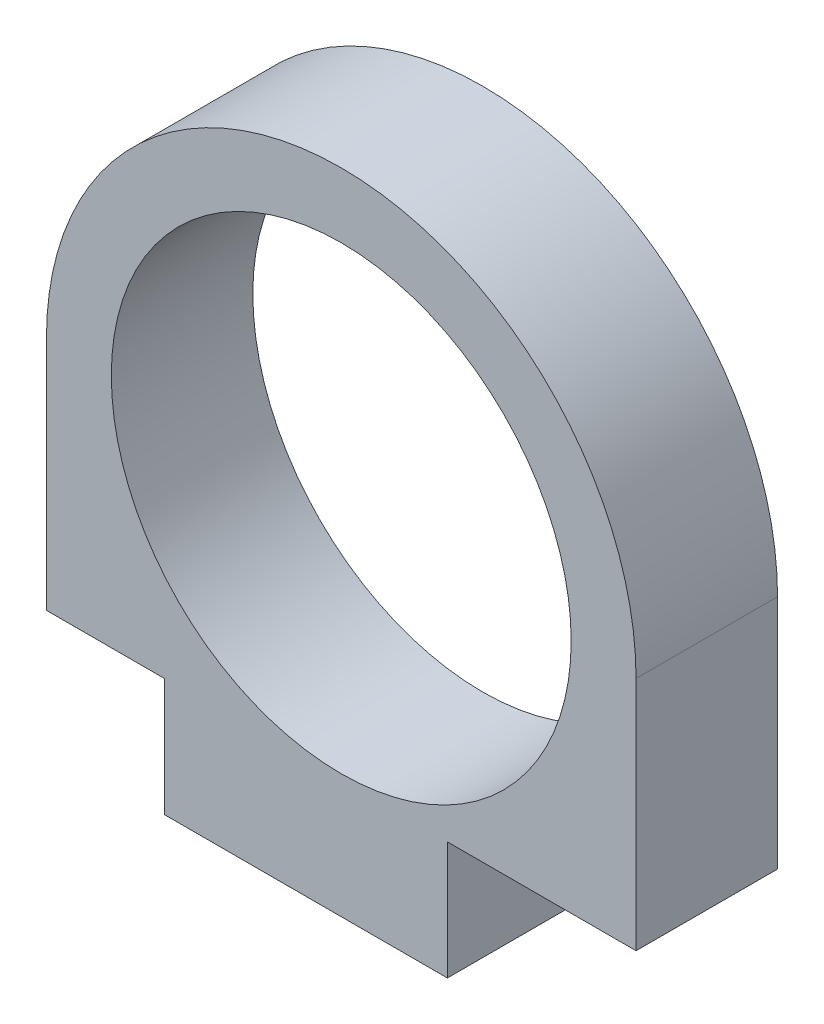
SolidWorks part; units mm, degrees
ref_plane "Alzado" through (0, 0, 0) normal (0, 0, 1) x (1, 0, 0)
ref_plane "Planta" through (0, 0, 0) normal (0, 1, 0) x (1, 0, 0)
ref_plane "Vista lateral" through (0, 0, 0) normal (1, 0, 0) x (0, 0, -1)
sketch "Croquis1" plane through (0, 0, 0) normal (0, 0, 1) x (1, 0, 0)
  line L0 (-12.5, -10) -> (12.5, -10) construction
  line L2 (-12.5, 0) -> (-12.5, -15)
  line L3 (-12.5, -15) -> (12.5, -15)
  line L4 (12.5, 0) -> (12.5, -15)
  line L6 (-12.5, -10) -> (-7.5, -10)
  line L7 (-12.5, -10) -> (-12.5, -15)
  line L8 (-12.5, -15) -> (-7.5, -15)
  line L9 (-7.5, -10) -> (-7.5, -15)
  line L10 (12.5, -10) -> (4.5, -10)
  line L11 (12.5, -10) -> (12.5, -15)
  line L12 (12.5, -15) -> (4.5, -15)
  line L13 (4.5, -10) -> (4.5, -15)
  arc A0 (12.5, 0) -> (-12.5, 0) centre (0, 0) ccw
  circle A1 centre (0, 0) radius 9.75
  point P13 (4.5, -12.5)
  dimension "D2" = 19.5
  dimension "D4" = 12.5
  dimension "D1" = 25
  dimension "D3" = 15
  dimension "D5" = 5
  dimension "D6" = 5
  dimension "D7" = 12
extrude "Saliente-Extruir1" add sketch "Croquis1" along normal blind 6 contours L6 L0 L10 L4 A0 L2 A1 | L0 L9 L3 L13
